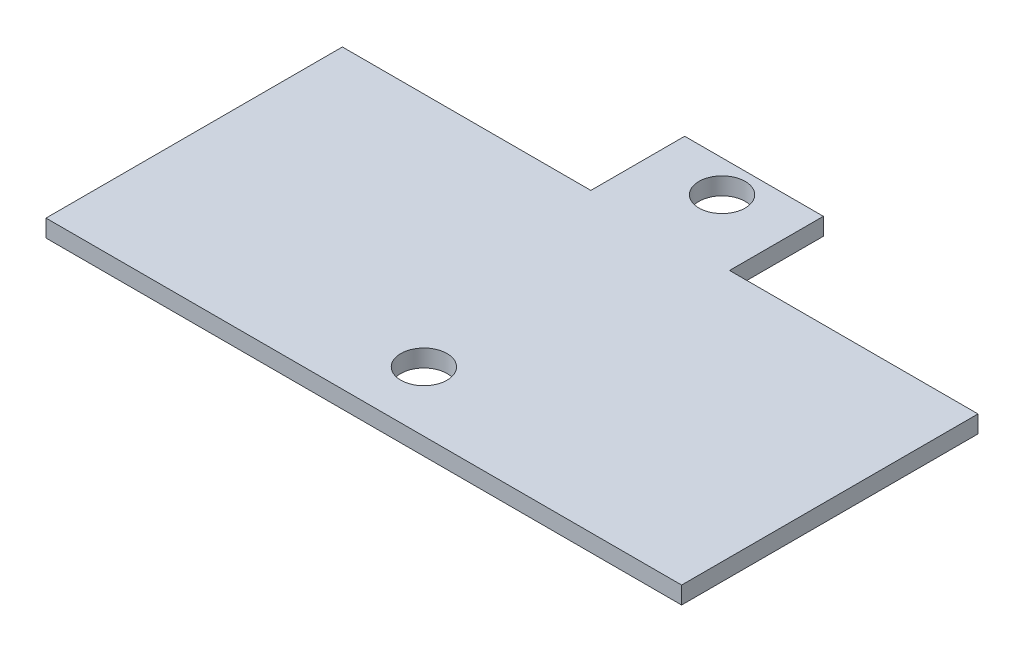
SolidWorks part; units mm, degrees
ref_plane "Спереди" through (0, 0, 0) normal (0, 0, 1) x (1, 0, 0)
ref_plane "Сверху" through (0, 0, 0) normal (0, 1, 0) x (1, 0, 0)
ref_plane "Справа" through (0, 0, 0) normal (1, 0, 0) x (0, 0, -1)
sketch "Эскиз1" plane through (0, 0, 0) normal (0, 1, 0) x (1, 0, 0)
  line L0 (0, 25.6465) -> (21.5, 25.6465)
  line L1 (0, 0) -> (55, 0)
  line L2 (0, 0) -> (0, 25.6465)
  line L4 (55, 0) -> (55, 25.6465)
  line L5 (21.5, 25.6465) -> (21.5, 33.7649)
  line L6 (21.5, 33.7649) -> (33.5, 33.7649)
  line L7 (33.5, 33.7649) -> (33.5, 25.6465)
  line L8 (33.5, 25.6465) -> (55, 25.6465)
  line L9 (27.5, 0) -> (27.5, 67.5298) construction
  circle A2 centre (27.5, 31) radius 2
  circle A3 centre (27.5, 5.2) radius 2
  point P13 (27.5, 33.7649)
extrude "Бобышка-Вытянуть1" add sketch "Эскиз1" along normal blind 1.5
